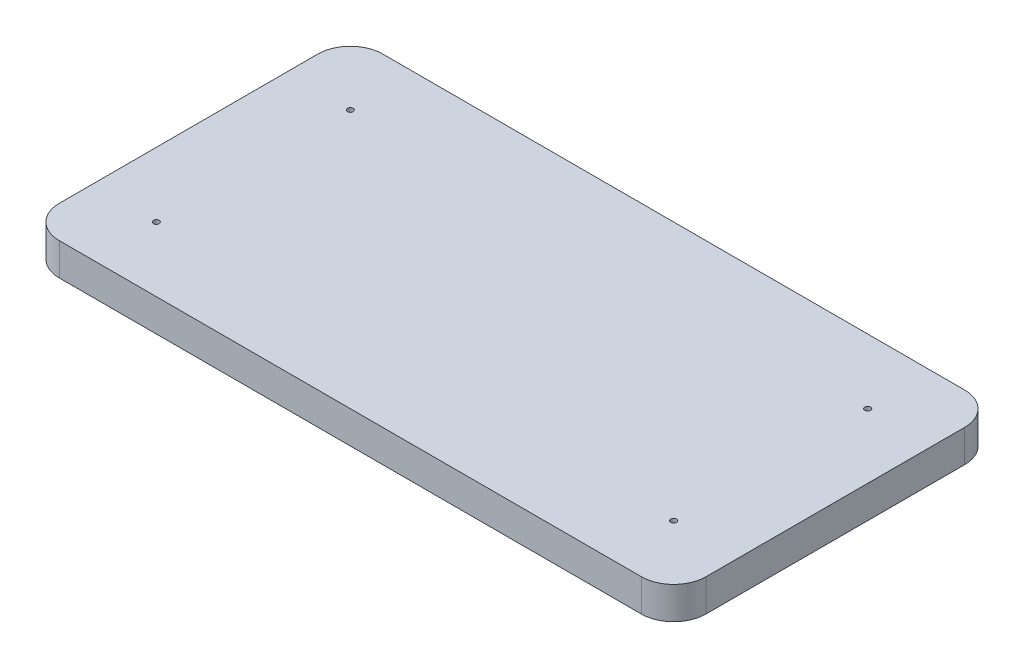
SolidWorks part; units mm, degrees
ref_plane "Front Plane" through (0, 0, 0) normal (0, 0, 1) x (1, 0, 0)
ref_plane "Top Plane" through (0, 0, 0) normal (0, 1, 0) x (1, 0, 0)
ref_plane "Right Plane" through (0, 0, 0) normal (1, 0, 0) x (0, 0, -1)
sketch "Sketch1" plane through (0, 0, 0) normal (0, 1, 0) x (1, 0, 0)
  line L1 (-2540, -1270) -> (2540, -1270)
  line L2 (-2540, -1270) -> (-2540, 1270)
  line L3 (-2540, 1270) -> (2540, 1270)
  line L4 (2540, -1270) -> (2540, 1270)
  line L5 (-2540, -1270) -> (2540, 1270) construction
  line L6 (-2540, 1270) -> (2540, -1270) construction
  point P0 (0, 0)
  dimension "D1" = 5080
  dimension "D2" = 2540
extrude "Boss-Extrude1" add sketch "Sketch1" along normal blind 254
sketch "Sketch3" plane through (0, 254, 0) normal (0, 1, 0) x (1, 0, 0)
  line L8 (2032, -762) -> (2032, 762)
  line L9 (2032, 762) -> (-2032, 762)
  line L10 (-2032, 762) -> (-2032, -762)
  line L11 (-2032, -762) -> (2032, -762)
  line L12 (2032, -762) -> (2032, 762)
  line L13 (2032, 762) -> (-2032, 762)
  line L14 (-2032, 762) -> (-2032, -762)
  line L15 (-2032, -762) -> (2032, -762)
  dimension "D1" = 508
hole_wizard "2-4.5 Tapped Hole1" positions "3DSketch4" profile "Sketch7" tap size "2-4.5" standard "ANSI Inch" end condition through all
sketch3d "3DSketch4"
  point P0 (-2032, 254, 762)
  point P3 (-2032, 254, -762)
  point P6 (2032, 254, -762)
  point P9 (2032, 254, 762)
sketch "Sketch7" plane through (-2032, 254, 762) normal (1, 0, 0) x (0, 0, 1)
  line L0 (0, 0) -> (0, 254)
  line L1 (0, 254) -> (22.6212, 254)
  line L2 (22.6212, 254) -> (22.6212, 0)
  line L5 (22.6212, 0) -> (0, 0)
  line L11 (0, -6.35) -> (0, 107.95) construction
  dimension "Thru Tap Drill Dia." = 45.2425
  dimension "Thru Tap Drill Depth" = 254
cosmetic thread "Hole Thread1" parameters "D2"=50.8
cosmetic thread "Hole Thread2" parameters "D2"=50.8
cosmetic thread "Hole Thread3" parameters "D2"=50.8
cosmetic thread "Hole Thread4" parameters "D2"=50.8
fillet "Fillet1" radius 254 4 edges at (-2540, 127, -1270) (-2540, 127, 1270) (2540, 127, -1270) (2540, 127, 1270)
